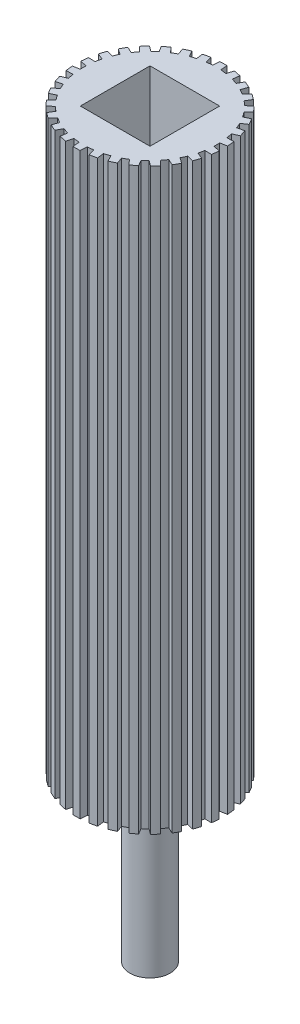
SolidWorks part; units mm, degrees
ref_plane "Front Plane" through (0, 0, 0) normal (0, 0, 1) x (1, 0, 0)
ref_plane "Top Plane" through (0, 0, 0) normal (0, 1, 0) x (1, 0, 0)
ref_plane "Right Plane" through (0, 0, 0) normal (1, 0, 0) x (0, 0, -1)
sketch "Sketch2" plane through (0, 0, 0) normal (0, 1, 0) x (1, 0, 0)
  line L1 (-0.7753, 12.6763) -> (-0.6703, 13.9539)
  line L2 (0.7753, 12.6763) -> (0.6703, 13.9539)
  line L3 (1.8772, 12.5605) -> (2.2456, 13.7883)
  line L4 (3.3939, 12.2381) -> (3.5568, 13.5096)
  line L5 (4.4476, 11.8957) -> (5.0633, 13.0201)
  line L6 (5.8642, 11.265) -> (6.2879, 12.4749)
  line L7 (6.8237, 10.7111) -> (7.6597, 11.6829)
  line L8 (8.0782, 9.7996) -> (8.7442, 10.895)
  line L9 (8.9015, 9.0583) -> (9.9213, 9.8351)
  line L10 (9.9391, 7.9059) -> (10.8183, 8.8389)
  line L11 (10.5903, 7.0096) -> (11.7493, 7.5574)
  line L12 (11.3657, 5.6667) -> (12.4196, 6.3965)
  line L13 (11.8163, 4.6546) -> (13.0638, 4.9494)
  line L14 (12.2955, 3.1798) -> (13.4781, 3.6745)
  line L15 (12.5258, 2.0961) -> (13.8074, 2.1252)
  line L16 (12.6879, 0.554) -> (13.9475, 0.792)
  line L17 (12.6879, -0.554) -> (13.9475, -0.792)
  line L18 (12.5258, -2.0961) -> (13.8074, -2.1252)
  line L19 (12.2955, -3.1798) -> (13.4781, -3.6745)
  line L20 (11.8163, -4.6546) -> (13.0638, -4.9494)
  line L21 (11.3657, -5.6667) -> (12.4196, -6.3965)
  line L22 (10.5903, -7.0096) -> (11.7493, -7.5574)
  line L23 (9.9391, -7.9059) -> (10.8183, -8.8389)
  line L24 (8.9015, -9.0583) -> (9.9213, -9.8351)
  line L25 (8.0782, -9.7996) -> (8.7442, -10.895)
  line L26 (6.8237, -10.7111) -> (7.6597, -11.6829)
  line L27 (5.8642, -11.265) -> (6.2879, -12.4749)
  line L28 (4.4476, -11.8957) -> (5.0633, -13.0201)
  line L29 (3.3939, -12.2381) -> (3.5568, -13.5096)
  line L30 (1.8772, -12.5605) -> (2.2456, -13.7883)
  line L31 (0.7753, -12.6763) -> (0.6703, -13.9539)
  line L32 (-0.7753, -12.6763) -> (-0.6703, -13.9539)
  line L33 (-1.8772, -12.5605) -> (-2.2456, -13.7883)
  line L34 (-3.3939, -12.2381) -> (-3.5568, -13.5096)
  line L35 (-4.4476, -11.8957) -> (-5.0633, -13.0201)
  line L36 (-5.8642, -11.265) -> (-6.2879, -12.4749)
  line L37 (-6.8237, -10.7111) -> (-7.6597, -11.6829)
  line L38 (-8.0782, -9.7996) -> (-8.7442, -10.895)
  line L39 (-8.9015, -9.0583) -> (-9.9213, -9.8351)
  line L40 (-9.9391, -7.9059) -> (-10.8183, -8.8389)
  line L41 (-10.5903, -7.0096) -> (-11.7493, -7.5574)
  line L42 (-11.3657, -5.6667) -> (-12.4196, -6.3965)
  line L43 (-11.8163, -4.6546) -> (-13.0638, -4.9494)
  line L44 (-12.2955, -3.1798) -> (-13.4781, -3.6745)
  line L45 (-12.5258, -2.0961) -> (-13.8074, -2.1252)
  line L46 (-12.6879, -0.554) -> (-13.9475, -0.792)
  line L47 (-12.6879, 0.554) -> (-13.9475, 0.792)
  line L48 (-12.5258, 2.0961) -> (-13.8074, 2.1252)
  line L49 (-12.2955, 3.1798) -> (-13.4781, 3.6745)
  line L50 (-11.8163, 4.6546) -> (-13.0638, 4.9494)
  line L51 (-11.3657, 5.6667) -> (-12.4196, 6.3965)
  line L52 (-10.5903, 7.0096) -> (-11.7493, 7.5574)
  line L53 (-9.9391, 7.9059) -> (-10.8183, 8.8389)
  line L54 (-8.9015, 9.0583) -> (-9.9213, 9.8351)
  line L55 (-8.0782, 9.7996) -> (-8.7442, 10.895)
  line L56 (-6.8237, 10.7111) -> (-7.6597, 11.6829)
  line L57 (-5.8642, 11.265) -> (-6.2879, 12.4749)
  line L58 (-4.4476, 11.8957) -> (-5.0633, 13.0201)
  line L59 (-3.3939, 12.2381) -> (-3.5568, 13.5096)
  line L60 (-1.8772, 12.5605) -> (-2.2456, 13.7883)
  arc A0 (-2.2456, 13.7883) -> (-3.5568, 13.5096) centre (0, 0) ccw
  arc A1 (-0.7753, 12.6763) -> (-1.8772, 12.5605) centre (0, 0) ccw
  arc A3 (-3.3939, 12.2381) -> (-4.4476, 11.8957) centre (0, 0) ccw
  arc A4 (-5.0633, 13.0201) -> (-6.2879, 12.4749) centre (0, 0) ccw
  arc A5 (-5.8642, 11.265) -> (-6.8237, 10.7111) centre (0, 0) ccw
  arc A6 (-7.6597, 11.6829) -> (-8.7442, 10.895) centre (0, 0) ccw
  arc A7 (-8.0782, 9.7996) -> (-8.9015, 9.0583) centre (0, 0) ccw
  arc A8 (-9.9213, 9.8351) -> (-10.8183, 8.8389) centre (0, 0) ccw
  arc A9 (-9.9391, 7.9059) -> (-10.5903, 7.0096) centre (0, 0) ccw
  arc A10 (-11.7493, 7.5574) -> (-12.4196, 6.3965) centre (0, 0) ccw
  arc A11 (-11.3657, 5.6667) -> (-11.8163, 4.6546) centre (0, 0) ccw
  arc A12 (-13.0638, 4.9494) -> (-13.4781, 3.6745) centre (0, 0) ccw
  arc A13 (-12.2955, 3.1798) -> (-12.5258, 2.0961) centre (0, 0) ccw
  arc A14 (-13.8074, 2.1252) -> (-13.9475, 0.792) centre (0, 0) ccw
  arc A15 (-12.6879, 0.554) -> (-12.6879, -0.554) centre (0, 0) ccw
  arc A16 (-13.9475, -0.792) -> (-13.8074, -2.1252) centre (0, 0) ccw
  arc A17 (-12.5258, -2.0961) -> (-12.2955, -3.1798) centre (0, 0) ccw
  arc A18 (-13.4781, -3.6745) -> (-13.0638, -4.9494) centre (0, 0) ccw
  arc A19 (-11.8163, -4.6546) -> (-11.3657, -5.6667) centre (0, 0) ccw
  arc A20 (-12.4196, -6.3965) -> (-11.7493, -7.5574) centre (0, 0) ccw
  arc A21 (-10.5903, -7.0096) -> (-9.9391, -7.9059) centre (0, 0) ccw
  arc A22 (-10.8183, -8.8389) -> (-9.9213, -9.8351) centre (0, 0) ccw
  arc A23 (-8.9015, -9.0583) -> (-8.0782, -9.7996) centre (0, 0) ccw
  arc A24 (-8.7442, -10.895) -> (-7.6597, -11.6829) centre (0, 0) ccw
  arc A25 (-6.8237, -10.7111) -> (-5.8642, -11.265) centre (0, 0) ccw
  arc A26 (-6.2879, -12.4749) -> (-5.0633, -13.0201) centre (0, 0) ccw
  arc A27 (-4.4476, -11.8957) -> (-3.3939, -12.2381) centre (0, 0) ccw
  arc A28 (-3.5568, -13.5096) -> (-2.2456, -13.7883) centre (0, 0) ccw
  arc A29 (-1.8772, -12.5605) -> (-0.7753, -12.6763) centre (0, 0) ccw
  arc A30 (-0.6703, -13.9539) -> (0.6703, -13.9539) centre (0, 0) ccw
  arc A31 (0.7753, -12.6763) -> (1.8772, -12.5605) centre (0, 0) ccw
  arc A32 (2.2456, -13.7883) -> (3.5568, -13.5096) centre (0, 0) ccw
  arc A33 (3.3939, -12.2381) -> (4.4476, -11.8957) centre (0, 0) ccw
  arc A34 (5.0633, -13.0201) -> (6.2879, -12.4749) centre (0, 0) ccw
  arc A35 (5.8642, -11.265) -> (6.8237, -10.7111) centre (0, 0) ccw
  arc A36 (7.6597, -11.6829) -> (8.7442, -10.895) centre (0, 0) ccw
  arc A37 (8.0782, -9.7996) -> (8.9015, -9.0583) centre (0, 0) ccw
  arc A38 (9.9213, -9.8351) -> (10.8183, -8.8389) centre (0, 0) ccw
  arc A39 (9.9391, -7.9059) -> (10.5903, -7.0096) centre (0, 0) ccw
  arc A40 (11.7493, -7.5574) -> (12.4196, -6.3965) centre (0, 0) ccw
  arc A41 (11.3657, -5.6667) -> (11.8163, -4.6546) centre (0, 0) ccw
  arc A42 (13.0638, -4.9494) -> (13.4781, -3.6745) centre (0, 0) ccw
  arc A43 (12.2955, -3.1798) -> (12.5258, -2.0961) centre (0, 0) ccw
  arc A44 (13.8074, -2.1252) -> (13.9475, -0.792) centre (0, 0) ccw
  arc A45 (12.6879, -0.554) -> (12.6879, 0.554) centre (0, 0) ccw
  arc A46 (13.9475, 0.792) -> (13.8074, 2.1252) centre (0, 0) ccw
  arc A47 (12.5258, 2.0961) -> (12.2955, 3.1798) centre (0, 0) ccw
  arc A48 (13.4781, 3.6745) -> (13.0638, 4.9494) centre (0, 0) ccw
  arc A49 (0.6703, 13.9539) -> (-0.6703, 13.9539) centre (0, 0) ccw
  arc A50 (3.5568, 13.5096) -> (2.2456, 13.7883) centre (0, 0) ccw
  arc A51 (6.2879, 12.4749) -> (5.0633, 13.0201) centre (0, 0) ccw
  arc A52 (8.7442, 10.895) -> (7.6597, 11.6829) centre (0, 0) ccw
  arc A53 (1.8772, 12.5605) -> (0.7753, 12.6763) centre (0, 0) ccw
  arc A54 (4.4476, 11.8957) -> (3.3939, 12.2381) centre (0, 0) ccw
  arc A55 (6.8237, 10.7111) -> (5.8642, 11.265) centre (0, 0) ccw
  arc A56 (8.9015, 9.0583) -> (8.0782, 9.7996) centre (0, 0) ccw
  arc A57 (10.5903, 7.0096) -> (9.9391, 7.9059) centre (0, 0) ccw
  arc A58 (10.8183, 8.8389) -> (9.9213, 9.8351) centre (0, 0) ccw
  arc A59 (12.4196, 6.3965) -> (11.7493, 7.5574) centre (0, 0) ccw
  arc A60 (11.8163, 4.6546) -> (11.3657, 5.6667) centre (0, 0) ccw
  point P129 (0, 0)
  dimension "D1" = 30
extrude "Boss-Extrude1" add sketch "Sketch2" along normal blind 211.1375 contours L39 A22 L40 A21 L41 A20 L42 A19 L43 A18 L44 A17 L45 A16 L46 A15 L47 A14 L48 A13 L49 A12 L50 A11 L51 A10 L52 A9 L53 A8 L54 A7 L55 A6 L56 A5 L57 A4 L58 A3 L59 A0 L60 A1 L1 A49 L2 A53 L3 A50 L4 A54 L5 A51 L6 A55 L7 A52 L8 A56 L9 A58 L10 A57 L11 A59 L12 A60 L13 A48 L14 A47 L15 A46 L16 A45 L17 A44 L18 A43 L19 A42 L20 A41 L21 A40 L22 A39 L23 A38 L24 A37 L25 A36 L26 A35 L27 A34 L28 A33 L29 A32 L30 A31 L31 A30 L32 A29 L33 A28 L34 A27 L35 A26 L36 A25 L37 A24 L38 A23
scale "Scale2" scale about centroid uniform scaling no x scale factor 0.96 y scale factor 1 z scale factor 0.96
sketch "Sketch3" plane through (0, 211.1375, 0) normal (0, 1, 0) x (1, 0, 0)
  circle A0 centre (0, 0) radius 3.6805
  dimension "D1" = 7.3609
extrude "Boss-Extrude2" add sketch "Sketch3" along normal blind 29.5593
sketch "Sketch4" plane through (0, 0, 0) normal (0, -1, 0) x (-1, 0, 0)
  circle A0 centre (0, 0) radius 3.6805
  dimension "D1" = 7.3609
extrude "Boss-Extrude3" add sketch "Sketch4" along normal blind 29.5593
sketch "Sketch6" plane through (0, 240.6968, 0) normal (0, 1, 0) x (1, 0, 0)
  circle A0 centre (0, 0) radius 20.6363
extrude "Cut-Extrude1" cut sketch "Sketch6" against normal blind 135.128 contours A0
sketch "Sketch7" plane through (0, 105.5688, 0) normal (0, 1, 0) x (1, 0, 0)
  line L1 (-6.35, -6.35) -> (6.35, -6.35)
  line L2 (-6.35, -6.35) -> (-6.35, 6.35)
  line L3 (-6.35, 6.35) -> (6.35, 6.35)
  line L4 (6.35, -6.35) -> (6.35, 6.35)
  line L5 (-6.35, -6.35) -> (6.35, 6.35) construction
  line L6 (-6.35, 6.35) -> (6.35, -6.35) construction
  point P0 (0, 0)
  dimension "D1" = 12.7
  dimension "D2" = 12.7
extrude "Cut-Extrude2" cut sketch "Sketch7" against normal blind 12.7
